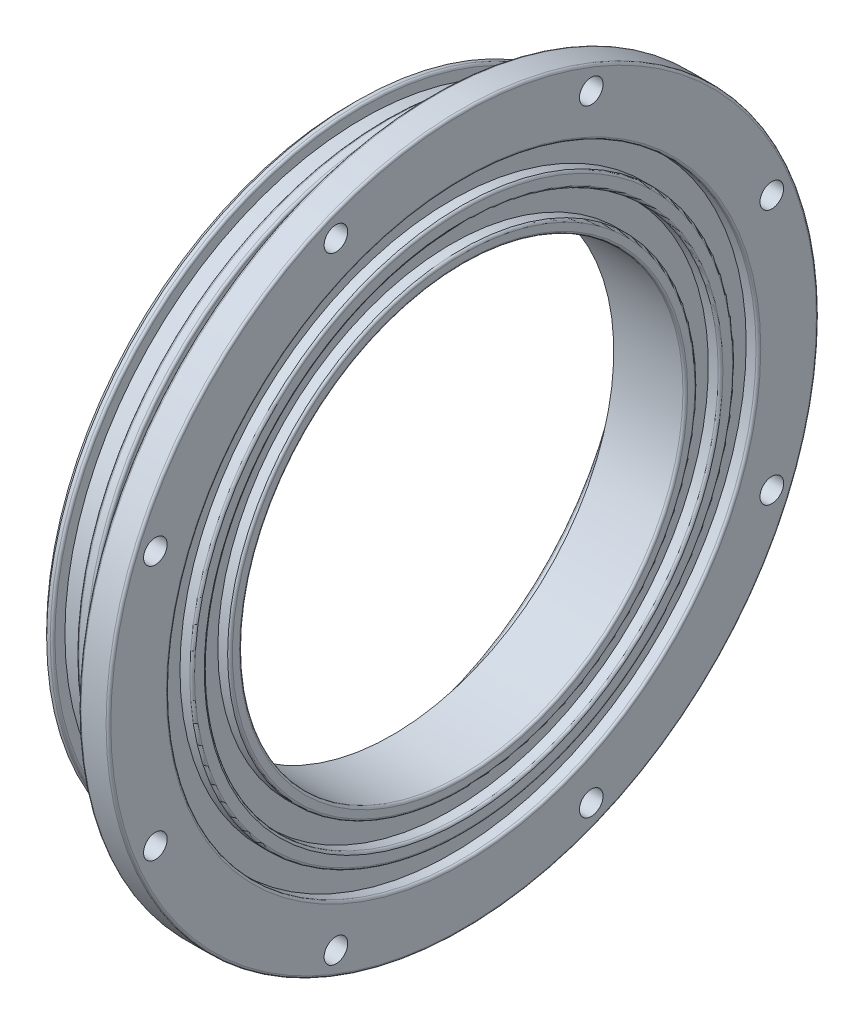
SolidWorks part; units mm, degrees
ref_plane "Front Plane" through (0, 0, 0) normal (0, 0, 1) x (1, 0, 0)
ref_plane "Top Plane" through (0, 0, 0) normal (0, 1, 0) x (1, 0, 0)
ref_plane "Right Plane" through (0, 0, 0) normal (1, 0, 0) x (0, 0, -1)
sketch "Sketch1" plane through (0, 0, 0) normal (0, 0, 1) x (1, 0, 0)
  line L0 (0, 0) -> (0, -58.42) construction
  line L5 (24.1999, -76) -> (17.8298, -76)
  line L6 (17.8298, -76) -> (17.8298, -66.421)
  line L7 (17.8298, -66.421) -> (0, -66.421) construction
  line L8 (0, -66.294) -> (0, -58.42)
  line L9 (0, -58.42) -> (8.89, -58.42)
  line L10 (0, -66.294) -> (2.54, -66.294)
  line L11 (2.54, -66.294) -> (2.54, -63.6575)
  line L12 (2.54, -63.6575) -> (7.6449, -63.6575)
  line L13 (7.6449, -63.6575) -> (7.6449, -66.294)
  line L14 (7.6449, -66.294) -> (10.1849, -66.294)
  line L15 (10.1849, -66.294) -> (10.1849, -63.6575)
  line L16 (10.1849, -63.6575) -> (15.2898, -63.6575)
  line L17 (15.2898, -63.6575) -> (15.2898, -66.294)
  line L18 (15.2898, -66.294) -> (17.8298, -66.294)
  line L19 (17.8298, -66.294) -> (17.8298, -66.421)
  line L20 (0, -66.421) -> (0, -66.294) construction
  line L24 (0, 0) -> (6.2477, 0) construction
  line L25 (8.89, -58.42) -> (8.89, -47.4495)
  line L26 (8.89, -47.4495) -> (24.1999, -47.4495)
  line L27 (24.1999, -47.4495) -> (24.1999, -49.9895)
  line L28 (24.1999, -49.9895) -> (21.59, -49.9895)
  line L29 (21.59, -49.9895) -> (21.59, -54.9896)
  line L30 (21.59, -54.9896) -> (24.1999, -54.9896)
  line L31 (24.1999, -54.9896) -> (24.1999, -58.0857)
  line L32 (24.1999, -58.0857) -> (21.59, -58.0857)
  line L33 (21.59, -58.0857) -> (21.59, -63.0858)
  line L34 (21.59, -63.0858) -> (24.1999, -63.0858)
  line L35 (24.1999, -63.0858) -> (24.1999, -76)
  dimension "CouplerIR" = 58.42
  dimension "76mm" = 76
  dimension "HullR" = 66.421
  dimension "RingSpacing" = 2.54
  dimension "GlandClearanceGap" = 0.254
  dimension "GlandWidth" = 5.1049
  dimension "D1" = 2.7635
  dimension "Planar Gland Backing Thickness" = 12.7
  dimension "OuterPlanarRingInnerRad" = 58.0857
  dimension "InnerPlanarRingInnerRad" = 49.9895
  dimension "PlanarGlandWidth" = 5.0001
  dimension "PlanarGlandDepth" = 2.6098
  dimension "D2" = 24.1999
revolve "Revolve1" add sketch "Sketch1" angle 360 about L24
chamfer "Chamfer1" distance 1.27 angle 45 1 edges at (0, 0, 66.294)
fillet "Fillet1" radius 0.508 13 edges at (0, 0, 58.42) (17.8298, 0, 76) (15.2898, 0, 66.294) (10.1849, 0, 66.294) (7.6449, 0, 66.294) (2.54, 0, 66.294) (8.89, 0, 58.42) (24.1999, 0, 76) (24.1999, 0, 63.0858) (24.1999, 0, 58.0857) (24.1999, 0, 54.9896) (24.1999, 0, 49.9895) (24.1999, 0, 47.4495)
sketch "Sketch3" plane through (24.1999, 0, 0) normal (1, 0, 0) x (0, 0, -1)
  line L1 (27.3185, -65.9527) -> (65.9527, -27.3185) construction
  line L2 (65.9527, -27.3185) -> (65.9527, 27.3185) construction
  line L3 (65.9527, 27.3185) -> (27.3185, 65.9527) construction
  line L4 (27.3185, 65.9527) -> (-27.3185, 65.9527) construction
  line L5 (-27.3185, 65.9527) -> (-65.9527, 27.3185) construction
  line L6 (-65.9527, 27.3185) -> (-65.9527, -27.3185) construction
  line L7 (-65.9527, -27.3185) -> (-27.3185, -65.9527) construction
  line L8 (-27.3185, -65.9527) -> (27.3185, -65.9527) construction
  circle A0 centre (0, 0) radius 65.9527 construction
  point P12 (-27.3185, 65.9527)
  point P13 (27.3185, 65.9527)
  point P14 (65.9527, 27.3185)
  point P15 (65.9527, -27.3185)
  point P16 (27.3185, -65.9527)
  point P17 (-27.3185, -65.9527)
  point P18 (-65.9527, -27.3185)
  point P19 (-65.9527, 27.3185)
  dimension "D1" = 142.7734
hole_wizard "#8 (0.199) Diameter Hole1" positions "Sketch3" profile "Sketch4" hole size "#8" standard "ANSI Inch"
sketch "Sketch4" plane through (24.1999, 27.3185, 65.9527) normal (0, 1, 0) x (0, 0, -1)
  line L0 (0, 0) -> (0, 10.668)
  line L1 (0, 10.668) -> (2.5273, 9.1494)
  line L2 (2.5273, 9.1494) -> (2.5273, 0)
  line L5 (2.5273, 0) -> (0, 0)
  line L10 (0, 10.668) -> (-2.5273, 9.1494) construction
  line L11 (0, -6.35) -> (0, 107.95) construction
  dimension "Hole Dia." = 5.0546
  dimension "Hole Depth" = 10.668
  dimension "Drill Angle" = 118
sketch "Sketch5" plane through (8.89, 0, 0) normal (-1, 0, 0) x (0, 0, 1)
  line L0 (-22.162, -53.5037) -> (-20.16, -48.6707) construction
  line L1 (20.16, -48.6707) -> (48.6707, -20.16) construction
  line L2 (48.6707, -20.16) -> (48.6707, 20.16) construction
  line L3 (48.6707, 20.16) -> (20.16, 48.6707) construction
  line L4 (20.16, 48.6707) -> (-20.16, 48.6707) construction
  line L5 (-20.16, 48.6707) -> (-48.6707, 20.16) construction
  line L6 (-48.6707, 20.16) -> (-48.6707, -20.16) construction
  line L7 (-48.6707, -20.16) -> (-20.16, -48.6707) construction
  line L8 (-20.16, -48.6707) -> (20.16, -48.6707) construction
  line L9 (-18.1581, -43.8376) -> (-20.16, -48.6707) construction
  line L10 (-18.1581, -43.8376) -> (-48.6707, -20.16) construction
  line L11 (20.16, -48.6707) -> (-18.1581, -43.8376) construction
  circle A0 centre (0, 0) radius 48.6707 construction
  circle A1 centre (0, 0) radius 57.912 construction
  circle A2 centre (0, 0) radius 47.4495 construction
  point P18 (-48.6707, -20.16)
  point P19 (-20.16, -48.6707)
  point P20 (20.16, -48.6707)
  point P21 (48.6707, -20.16)
  point P22 (48.6707, 20.16)
  point P23 (20.16, 48.6707)
  point P24 (-20.16, 48.6707)
  point P25 (-48.6707, 20.16)
hole_wizard "#4-40 Tapped Hole1" positions "Sketch5" profile "Sketch6" tap size "#4-40" standard "ANSI Inch"
sketch "Sketch6" plane through (8.89, 20.16, -48.6707) normal (0, 1, 0) x (0, 0, 1)
  line L0 (0, 0) -> (0, 7.62)
  line L1 (0, 7.62) -> (1.1303, 6.9408)
  line L2 (1.1303, 6.9408) -> (1.1303, 0)
  line L5 (1.1303, 0) -> (0, 0)
  line L10 (0, 7.62) -> (-1.1303, 6.9408) construction
  line L11 (0, -6.35) -> (0, 107.95) construction
  dimension "Tap Drill Dia." = 2.2606
  dimension "Tap Drill Depth" = 7.62
  dimension "Drill Angle" = 118
cosmetic thread "Hole Thread1" parameters "D1"=5.588, "D2"=2.8448
cosmetic thread "Hole Thread2" parameters "D1"=5.588, "D2"=2.8448
cosmetic thread "Hole Thread3" parameters "D1"=5.588, "D2"=2.8448
cosmetic thread "Hole Thread4" parameters "D1"=5.588, "D2"=2.8448
cosmetic thread "Hole Thread5" parameters "D1"=5.588, "D2"=2.8448
cosmetic thread "Hole Thread6" parameters "D1"=5.588, "D2"=2.8448
cosmetic thread "Hole Thread7" parameters "D1"=5.588, "D2"=2.8448
cosmetic thread "Hole Thread8" parameters "D1"=5.588, "D2"=2.8448
equation "\"HullID\"= 5.230"
equation "\"HullIR\"= \"HullID\" / 2"
equation "\"CrossSectionThickness\"= .136"
equation "\"RingCompression\"= .2"
equation "\"GlandDepth\"= \"CrossSectionThickness\" * ( 1 - \"RingCompression\" )"
equation "\"D1@Sketch1\"=\"GlandDepth\""
equation "\"HullR@Sketch1\"= \"HullIR\""
equation "\"RingCSArea\"= .0164"
equation "\"GlandFill\"= .75"
equation "\"GlandWidth\"= 1 / \"GlandFill\" * \"RingCSArea\" / \"GlandDepth\""
equation "\"GlandWidth@Sketch1\"= \"GlandWidth\""
equation "\"OuterPlanarRingNomInnerDiameter\"= 4.484"
equation "\"PlanarRingStreching\"= .02"
equation "\"PlanarRingCrosssectionDepth\"= .137"
equation "\"OuterPlanarRingInnerRad\"= \"OuterPlanarRingNomInnerDiameter\" * ( 1 + \"PlanarRingStreching\" ) / 2"
equation "\"OuterPlanarRingInnerRad@Sketch1\"= \"OuterPlanarRingInnerRad\""
equation "\"PlanarRingCommpression\"= .25"
equation "\"PlanarRingGlandDepth\"= \"PlanarRingCrosssectionDepth\" * ( 1 - \"PlanarRingCommpression\" )"
equation "\"PlanarRingCrossSectionalArea\"= .01517"
equation "\"PlanarGlandFill\"= .75"
equation "\"PlanarGlandWidth\"= \"PlanarRingCrossSectionalArea\" / \"PlanarGlandFill\" / \"PlanarRingGlandDepth\""
equation "\"PlanarGlandWidth@Sketch1\"= \"PlanarGlandWidth\""
equation "\"PlanarGlandDepth@Sketch1\"= \"PlanarRingGlandDepth\""
equation "\"InnerPlanarRingNomInnerDiameter\"= 3.859"
equation "\"InnerPlanarRingInnerRad\"= \"InnerPlanarRingNomInnerDiameter\" * ( 1 + \"PlanarRingStreching\" ) / 2"
equation "\"InnerPlanarRingInnerRad@Sketch1\"= \"InnerPlanarRingInnerRad\""
